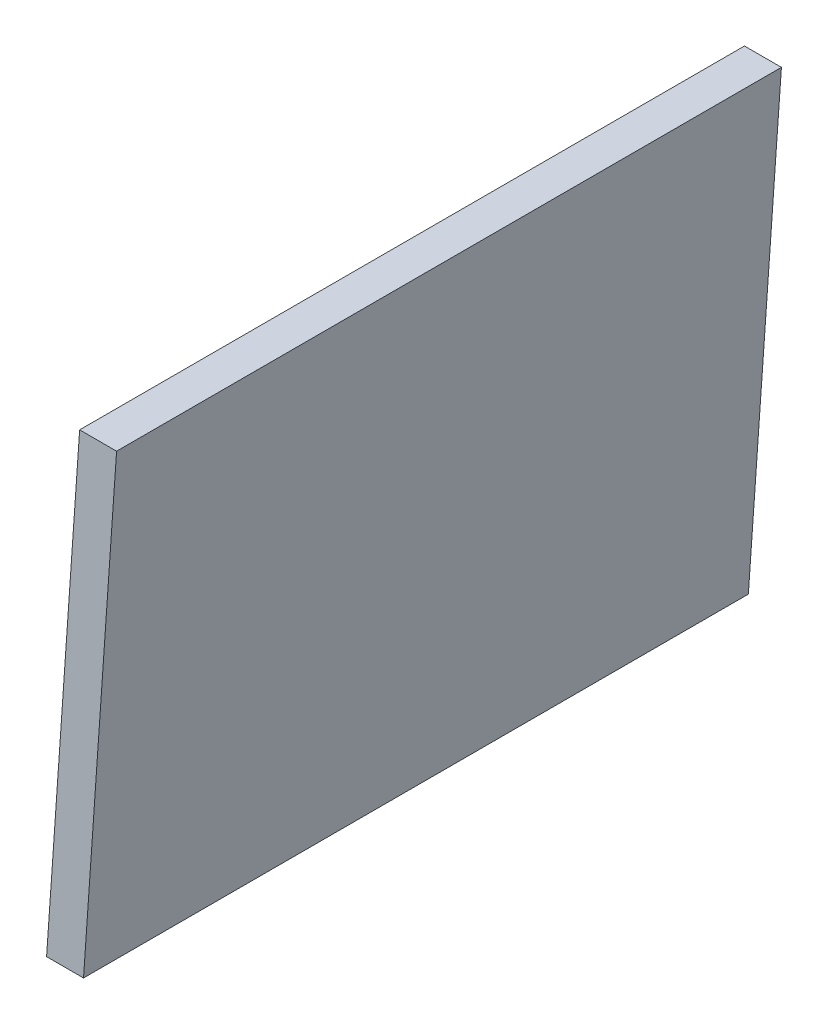
SolidWorks part; units mm, degrees
ref_plane "Front Plane" through (0, 0, 0) normal (0, 0, 1) x (1, 0, 0)
ref_plane "Top Plane" through (0, 0, 0) normal (0, 1, 0) x (1, 0, 0)
ref_plane "Right Plane" through (0, 0, 0) normal (1, 0, 0) x (0, 0, -1)
sketch "Sketch1" plane through (0, 0, 0) normal (0, 0, 1) x (1, 0, 0)
  line L0 (0, 0) -> (22.3766, 320)
  line L2 (47.3766, 320) -> (25, 0)
  line L3 (25, 0) -> (0, 0)
  line L4 (0, 0) -> (0, 64.123) construction
  line L5 (22.3766, 320) -> (47.3766, 320)
  dimension "D1" = 4
  dimension "D2" = 25
  dimension "D3" = 320
  dimension "D4" = 25
extrude "Boss-Extrude1" add sketch "Sketch1" along normal blind 450
